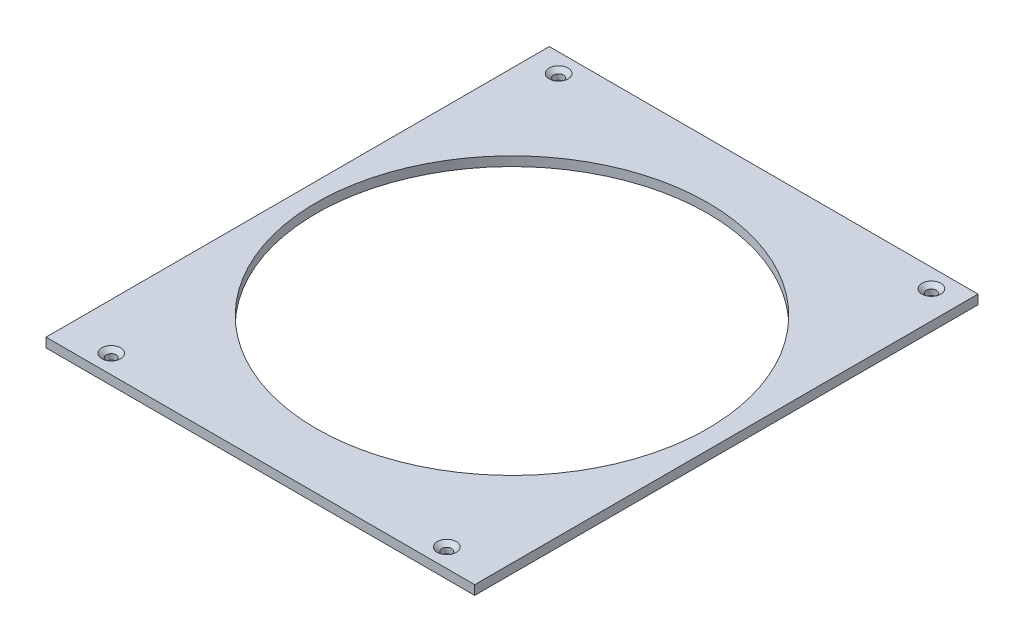
SolidWorks part; units mm, degrees
material "6061-T6 (SS)"
ref_plane "Front Plane" through (0, 0, 0) normal (0, 0, 1) x (1, 0, 0)
ref_plane "Top Plane" through (0, 0, 0) normal (0, 1, 0) x (1, 0, 0)
ref_plane "Right Plane" through (0, 0, 0) normal (1, 0, 0) x (0, 0, -1)
sketch "Sketch1" plane through (0, 0, 0) normal (0, 1, 0) x (1, 0, 0)
  line L0 (0, 0) -> (0, 133.35) construction
  line L1 (0, 133.35) -> (0, 171.45) construction
  line L2 (0, 171.45) -> (146.05, 171.45)
  line L3 (133.35, 0) -> (146.05, 0) construction
  line L4 (146.05, 0) -> (146.05, 171.45)
  line L6 (0, 171.45) -> (-146.05, 171.45)
  line L7 (-146.05, 171.45) -> (-146.05, 0)
  line L8 (133.35, 0) -> (-146.05, 0) construction
  line L9 (-146.05, 0) -> (-146.05, -171.45)
  line L10 (-146.05, -171.45) -> (146.05, -171.45)
  line L11 (146.05, -171.45) -> (146.05, 0)
  line L12 (0, -133.35) -> (0, -171.45) construction
  circle A0 centre (0, 0) radius 133.35
  point P8 (-133.35, 0)
  dimension "D1" = 266.7
  dimension "D2" = 12.7
  dimension "D3" = 38.1
  dimension "D5" = 12.7
  dimension "D6" = 38.1
extrude "Extrude & center hole" add sketch "Sketch1" along normal blind 6.35
hole_wizard "CSK for 1/4 Flat Head Machine Screw (100)1" positions "Sketch4" profile "Sketch5" countersink size "1/4" standard "ANSI Inch" end condition through all
sketch "Sketch4" plane through (0, 6.35, 0) normal (0, 1, 0) x (1, 0, 0)
  line L0 (-146.05, -171.45) -> (146.05, -171.45) construction
  line L2 (146.05, -171.45) -> (146.05, 171.45) construction
  line L3 (146.05, 171.45) -> (-146.05, 171.45) construction
  line L6 (-146.05, 171.45) -> (-146.05, -171.45) construction
  point P0 (-114.3, -158.75)
  point P2 (114.3, -158.75)
  point P4 (127, 158.75)
  point P6 (-127, 158.75)
  dimension "D1" = 12.7
  dimension "D2" = 31.75
  dimension "D3" = 31.75
  dimension "D4" = 12.7
  dimension "D5" = 12.7
  dimension "D6" = 19.05
  dimension "D7" = 12.7
  dimension "D8" = 19.05
sketch "Sketch5" plane through (-114.3, 6.35, 158.75) normal (1, 0, 0) x (0, 0, 1)
  line L0 (0, 0) -> (0, 6.35)
  line L1 (0, 6.35) -> (3.3782, 6.35)
  line L2 (3.3782, 6.35) -> (3.3782, 2.5682)
  line L3 (3.3782, 2.5682) -> (6.4389, 0)
  line L5 (6.4389, 0) -> (0, 0)
  line L6 (-3.3782, 2.5682) -> (-6.4389, 0) construction
  line L11 (0, -6.35) -> (0, 107.95) construction
  dimension "Thru Hole Dia." = 6.7564
  dimension "Thru Hole Depth" = 6.35
  dimension "Near C'Sink Dia." = 12.8778
  dimension "Near C'Sink Angle" = 100
